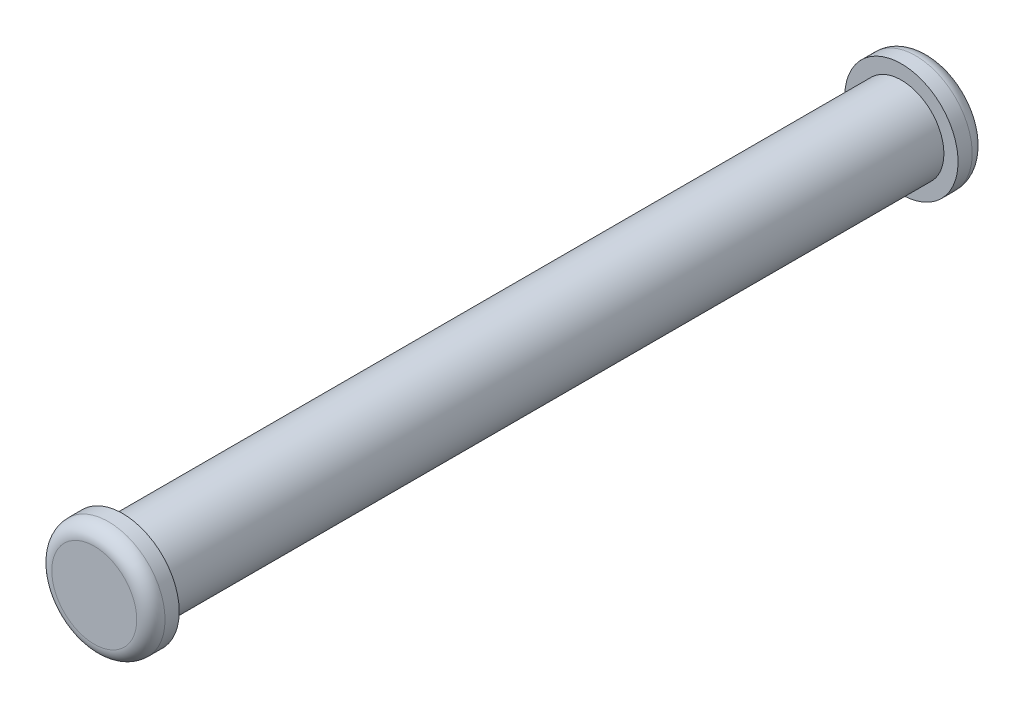
SolidWorks part; units mm, degrees
ref_plane "Front Plane" through (0, 0, 0) normal (0, 0, 1) x (1, 0, 0)
ref_plane "Top Plane" through (0, 0, 0) normal (0, 1, 0) x (1, 0, 0)
ref_plane "Right Plane" through (0, 0, 0) normal (1, 0, 0) x (0, 0, -1)
sketch "Sketch1" plane through (0, 0, 0) normal (0, 0, 1) x (1, 0, 0)
  circle A0 centre (0, 0) radius 1.5
  dimension "D1" = 3
extrude "Boss-Extrude1" add sketch "Sketch1" along normal blind 27.5
sketch "Sketch2" plane through (0, 0, 0) normal (0, 0, -1) x (-1, 0, 0)
  circle A0 centre (0, 0) radius 2
  dimension "D1" = 4
extrude "Boss-Extrude2" add sketch "Sketch2" along normal blind 1
sketch "Sketch3" plane through (0, 0, 27.5) normal (0, 0, 1) x (1, 0, 0)
  circle A1 centre (0, 0) radius 2
  circle A2 centre (0, 0) radius 2
  dimension "D1" = 0
extrude "Boss-Extrude3" add sketch "Sketch3" along normal blind 1
fillet "Fillet1" radius 0.5 2 edges at (-2, 0, -1) (2, 0, 28.5)
